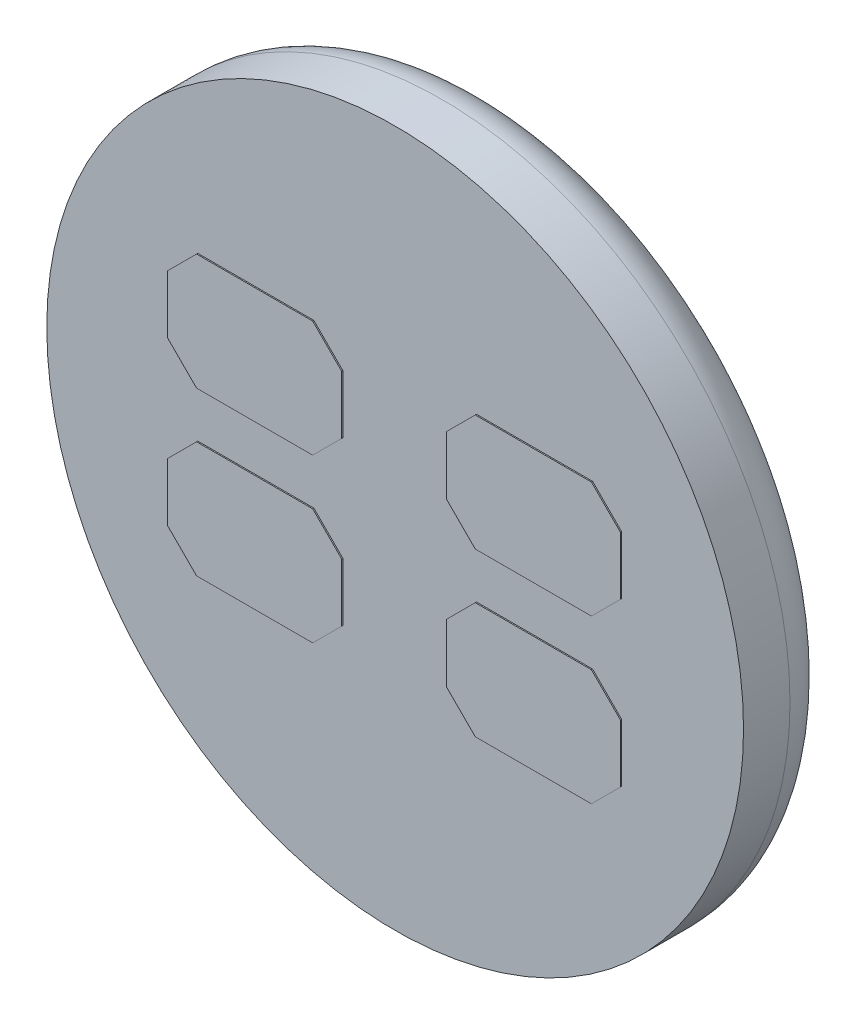
SolidWorks part; units mm, degrees
ref_plane "Front" through (0, 0, 0) normal (0, 0, 1) x (1, 0, 0)
ref_plane "Top" through (0, 0, 0) normal (0, 1, 0) x (1, 0, 0)
ref_plane "Right" through (0, 0, 0) normal (1, 0, 0) x (0, 0, -1)
sketch "草图1" plane through (0, 0, 0) normal (0, 0, 1) x (1, 0, 0)
  circle A0 centre (0, 0) radius 3
  dimension "D1" = 6
extrude "凸台-拉伸1" add sketch "草图1" along normal blind 0.8
sketch "草图2" plane through (0, 0, 0) normal (0, 0, -1) x (-1, 0, 0)
  circle A0 centre (0, 0) radius 0.3
  circle A1 centre (0, 0) radius 0.45
  circle A2 centre (0, 0) radius 0.85
  circle A3 centre (0, 0) radius 1.05
  circle A4 centre (0, 0) radius 1.55
  circle A5 centre (0, 0) radius 1.7
  circle A6 centre (0, 0) radius 2.2
  dimension "D1" = 0.6
  dimension "D2" = 0.9
  dimension "D3" = 1.7
  dimension "D4" = 2.1
  dimension "D5" = 3.1
  dimension "D6" = 3.4
  dimension "D7" = 4.4
extrude "凸台-拉伸2" add sketch "草图2" along normal blind 0.01 contours A0 | A2 A1 | A4 A3 | A6 A5
sketch "草图3" plane through (0, 0, 0.8) normal (0, 0, 1) x (1, 0, 0)
  line L0 (-1000, 0) -> (49000, 0) construction
  line L1 (0.45, -0.45) -> (0.7, -0.2)
  line L2 (0.7, 1.2) -> (1.7, 1.2)
  line L3 (0.45, 0.95) -> (0.45, 0.45)
  line L4 (0.7, 0.2) -> (1.7, 0.2)
  line L5 (0, -1000) -> (0, 49000) construction
  line L6 (1.95, 0.95) -> (1.95, 0.45)
  line L7 (1.7, -0.2) -> (0.7, -0.2)
  line L8 (1.95, -0.45) -> (1.7, -0.2)
  line L9 (1.7, -1.2) -> (1.95, -0.95)
  line L10 (0.45, 0.95) -> (0.7, 1.2)
  line L11 (1.7, 1.2) -> (1.95, 0.95)
  line L12 (1.95, 0.45) -> (1.7, 0.2)
  line L13 (1.7, 0.2) -> (0.7, 0.2)
  line L14 (0.45, 0.45) -> (0.7, 0.2)
  line L15 (0.45, -0.95) -> (0.7, -1.2)
  line L16 (1.95, -0.95) -> (1.95, -0.45)
  line L17 (0.7, -0.2) -> (1.7, -0.2)
  line L18 (0.45, -0.95) -> (0.45, -0.45)
  line L19 (0.7, -1.2) -> (1.7, -1.2)
  line L20 (-0.7, -1.2) -> (-1.7, -1.2)
  line L21 (-0.45, -0.95) -> (-0.45, -0.45)
  line L22 (-0.7, -0.2) -> (-1.7, -0.2)
  line L23 (-1.95, -0.95) -> (-1.95, -0.45)
  line L24 (-0.45, -0.95) -> (-0.7, -1.2)
  line L25 (-0.45, 0.45) -> (-0.7, 0.2)
  line L26 (-1.7, 0.2) -> (-0.7, 0.2)
  line L27 (-1.95, 0.45) -> (-1.7, 0.2)
  line L28 (-1.7, 1.2) -> (-1.95, 0.95)
  line L29 (-0.45, 0.95) -> (-0.7, 1.2)
  line L30 (-1.7, -1.2) -> (-1.95, -0.95)
  line L31 (-1.95, -0.45) -> (-1.7, -0.2)
  line L32 (-1.7, -0.2) -> (-0.7, -0.2)
  line L33 (-1.95, 0.95) -> (-1.95, 0.45)
  line L34 (-0.7, 0.2) -> (-1.7, 0.2)
  line L35 (-0.45, 0.95) -> (-0.45, 0.45)
  line L36 (-0.7, 1.2) -> (-1.7, 1.2)
  line L37 (-0.45, -0.45) -> (-0.7, -0.2)
  dimension "D3" = 0.2
  dimension "D4" = 0.45
extrude "凸台-拉伸3" add sketch "草图3" along normal blind 0.01 contours L29 L36 L28 L33 L27 L26 L25 L35 | L3 L14 L4 L12 L6 L11 L2 L10 | L15 L19 L9 L16 L8 L7 L1 L18 | L21 L37 L22 L31 L23 L30 L20 L24
fillet "圆角2" radius 0.4 1 edges at (3, 0, 0)
